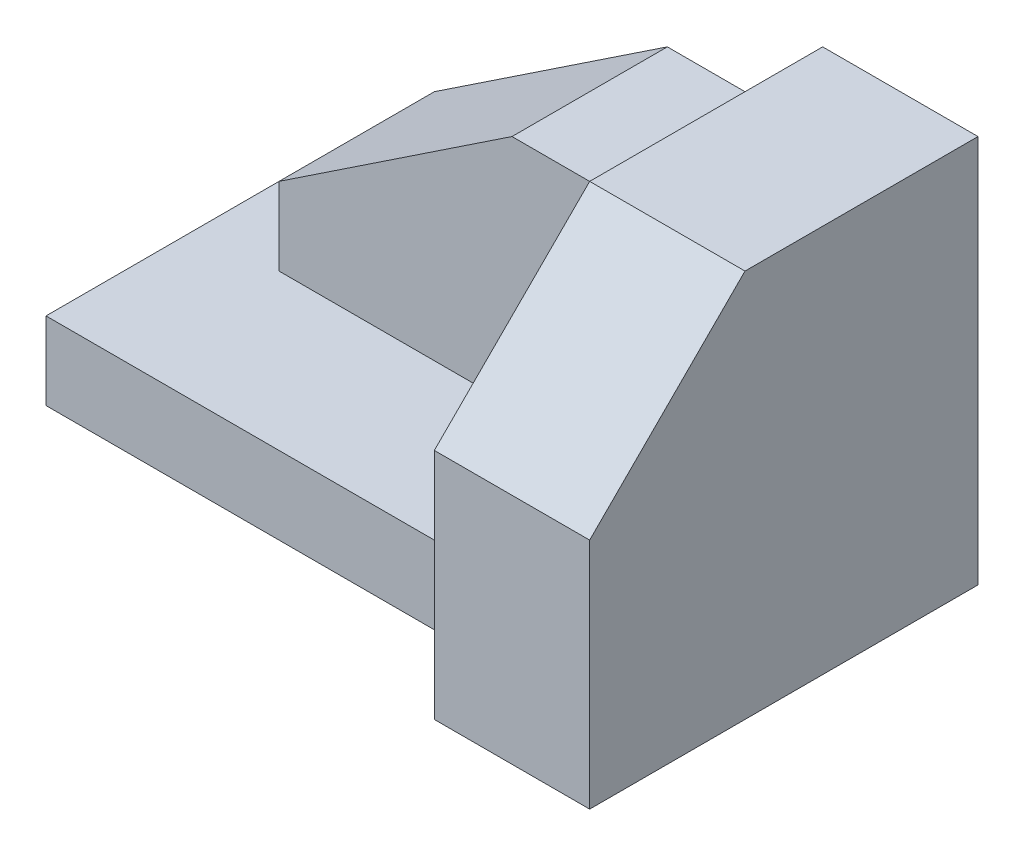
SolidWorks part; units mm, degrees
ref_plane "Front Plane" through (0, 0, 0) normal (0, 0, 1) x (1, 0, 0)
ref_plane "Top Plane" through (0, 0, 0) normal (0, 1, 0) x (1, 0, 0)
ref_plane "Right Plane" through (0, 0, 0) normal (1, 0, 0) x (0, 0, -1)
sketch "Sketch2" plane through (0, 0, 0) normal (0, 1, 0) x (1, 0, 0)
  line L0 (0, 10) -> (60, 10)
  line L1 (0, 0) -> (80, 0)
  line L2 (0, 0) -> (0, 50)
  line L3 (0, 50) -> (80, 50)
  line L4 (80, 0) -> (80, 50)
  line L5 (60, 10) -> (60, 0)
  point P10 (-33.3981, 14.5631)
  dimension "D1" = 80
  dimension "D2" = 50
  dimension "D3" = 20
  dimension "D4" = 60
  dimension "D5" = 10
extrude "Boss-Extrude1" add sketch "Sketch2" along normal blind 10 contours L0 L5 L1 L4 L3 L2
sketch "Sketch3" plane through (0, 10, 0) normal (0, 1, 0) x (1, 0, 0)
  line L1 (80, 50) -> (60, 50)
  line L2 (80, 50) -> (80, 0)
  line L3 (80, 0) -> (60, 0)
  line L4 (60, 50) -> (60, 0)
extrude "Boss-Extrude2" add sketch "Sketch3" along normal blind 40
sketch "Sketch4" plane through (80, 0, 0) normal (1, 0, 0) x (0, 0, -1)
  line L0 (20, 50) -> (0, 30)
  line L1 (0, 50) -> (50, 50) construction
  line L2 (0, 50) -> (0, 0) construction
  line L3 (0, 30) -> (0, 50)
  line L4 (0, 50) -> (20, 50)
  dimension "D1" = 20
  dimension "D2" = 20
extrude "Cut-Extrude1" cut sketch "Sketch4" against normal blind 40
sketch "Sketch5" plane through (0, 10, 0) normal (0, 1, 0) x (1, 0, 0)
  line L1 (60, 50) -> (10, 50)
  line L2 (60, 50) -> (60, 30)
  line L3 (60, 30) -> (10, 30)
  line L4 (10, 50) -> (10, 30)
  dimension "D1" = 10
  dimension "D2" = 20
extrude "Boss-Extrude3" add sketch "Sketch5" along normal blind 30
sketch "Sketch6" plane through (0, 0, -30) normal (0, 0, 1) x (1, 0, 0)
  line L0 (40, 40) -> (10, 20)
  line L1 (10, 40) -> (60, 40) construction
  line L2 (10, 40) -> (10, 10) construction
  line L3 (10, 20) -> (10, 40)
  line L4 (10, 40) -> (40, 40)
  dimension "D1" = 10
  dimension "D2" = 20
extrude "Cut-Extrude2" cut sketch "Sketch6" against normal blind 30
